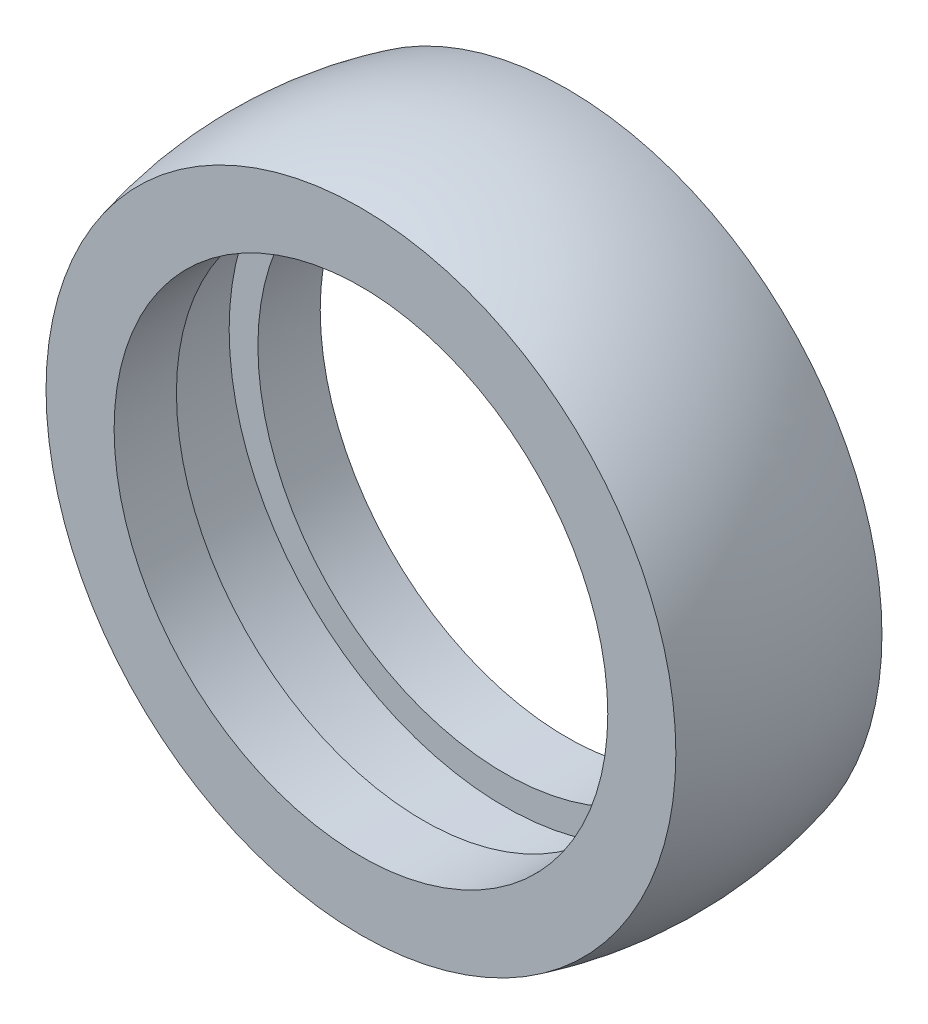
SolidWorks part; units mm, degrees
ref_plane "Front Plane" through (0, 0, 0) normal (0, 0, 1) x (1, 0, 0)
ref_plane "Top Plane" through (0, 0, 0) normal (0, 1, 0) x (1, 0, 0)
ref_plane "Right Plane" through (0, 0, 0) normal (1, 0, 0) x (0, 0, -1)
sketch "Sketch1" plane through (0, 0, 0) normal (1, 0, 0) x (0, 0, -1)
  line L0 (-733.316, 0) -> (35932.4843, 0) construction
  line L1 (0, -733.316) -> (0, 35932.4843) construction
  line L2 (-10.75, 25.75) -> (-4.25, 25.75)
  line L3 (-4.25, 25.75) -> (-4.25, 28.75)
  line L4 (-4.25, 28.75) -> (4.25, 28.75)
  line L5 (4.25, 28.75) -> (4.25, 25.75)
  line L6 (4.25, 25.75) -> (10.75, 25.75)
  line L7 (10.75, 25.75) -> (10.75, 32.851)
  line L8 (-10.75, 25.75) -> (-10.75, 32.851)
  arc A0 (-10.75, 32.851) -> (10.75, 32.851) centre (0, -7.75) cw
  point P14 (0, 28.75)
  point P15 (9.8751, 24.0901)
  point P16 (-9.938, 32.7701)
  point P17 (12.5168, 31.9524)
  point P18 (0, 34.25)
  dimension "D7" = 42
  dimension "D1" = 68.5
  dimension "D2" = 8.5
  dimension "D3" = 8.5
  dimension "D4" = 51.5
  dimension "D5" = 21.5
  dimension "D6" = 3
  dimension "D8" = 57.5
revolve "Revolve1" add sketch "Sketch1" angle 360 about L0
